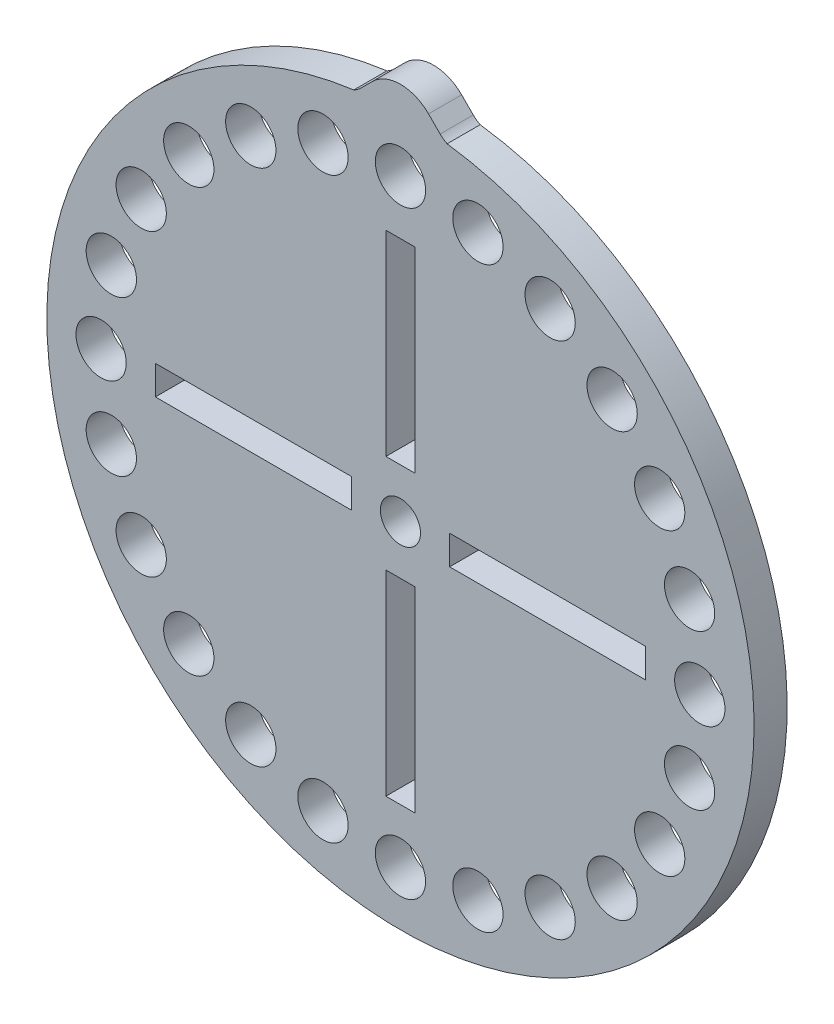
SolidWorks part; units mm, degrees
ref_plane "Front Plane" through (0, 0, 0) normal (0, 0, 1) x (1, 0, 0)
ref_plane "Top Plane" through (0, 0, 0) normal (0, 1, 0) x (1, 0, 0)
ref_plane "Right Plane" through (0, 0, 0) normal (1, 0, 0) x (0, 0, -1)
sketch "Sketch1" plane through (0, 0, 0) normal (0, 0, 1) x (1, 0, 0)
  line L0 (0, 31.26) -> (0, 33.8) construction
  line L1 (0, 28.72) -> (2.5183, 28.3885) construction
  line L2 (2.5183, 28.3885) -> (4.915, 28.0729) construction
  line L3 (4.915, 28.0729) -> (7.4333, 27.7414) construction
  line L4 (0, 2.05) -> (0, 4.59) construction
  line L5 (-0.1778, 26.1862) -> (0.1778, 26.1862) construction
  line L6 (-0.1778, 26.1862) -> (-0.1778, 30.9862) construction
  line L7 (-0.1778, 30.9862) -> (0.1778, 30.9862) construction
  line L8 (0.1778, 26.1862) -> (0.1778, 30.9862) construction
  line L9 (-1.524, 23.64) -> (1.524, 23.64)
  line L10 (-1.524, 23.64) -> (-1.524, 4.59)
  line L11 (-1.524, 4.59) -> (1.524, 4.59)
  line L12 (1.524, 23.64) -> (1.524, 4.59)
  line L13 (0, 26.18) -> (0, 23.64) construction
  line L14 (23.64, 1.524) -> (23.64, -1.524)
  line L15 (23.64, 1.524) -> (4.59, 1.524)
  line L16 (23.64, -1.524) -> (4.59, -1.524)
  line L17 (4.59, 1.524) -> (4.59, -1.524)
  line L18 (1.524, -23.64) -> (-1.524, -23.64)
  line L19 (1.524, -23.64) -> (1.524, -4.59)
  line L20 (-1.524, -23.64) -> (-1.524, -4.59)
  line L21 (1.524, -4.59) -> (-1.524, -4.59)
  line L22 (-23.64, -1.524) -> (-23.64, 1.524)
  line L23 (-23.64, -1.524) -> (-4.59, -1.524)
  line L24 (-23.64, 1.524) -> (-4.59, 1.524)
  line L25 (-4.59, -1.524) -> (-4.59, 1.524)
  circle A0 centre (0, 0) radius 33.8
  circle A1 centre (14.36, 24.8722) radius 2.54
  circle A2 centre (20.3081, 20.3081) radius 2.54
  circle A3 centre (24.8722, 14.36) radius 2.54
  circle A4 centre (27.7414, 7.4333) radius 2.54
  circle A5 centre (28.72, 0) radius 2.54
  circle A6 centre (27.7414, -7.4333) radius 2.54
  circle A7 centre (24.8722, -14.36) radius 2.54
  circle A8 centre (20.3081, -20.3081) radius 2.54
  circle A9 centre (14.36, -24.8722) radius 2.54
  circle A10 centre (7.4333, -27.7414) radius 2.54
  circle A11 centre (0, -28.72) radius 2.54
  circle A12 centre (-7.4333, -27.7414) radius 2.54
  circle A13 centre (-14.36, -24.8722) radius 2.54
  circle A14 centre (-20.3081, -20.3081) radius 2.54
  circle A15 centre (-24.8722, -14.36) radius 2.54
  circle A16 centre (-27.7414, -7.4333) radius 2.54
  circle A17 centre (-28.72, 0) radius 2.54
  circle A18 centre (-27.7414, 7.4333) radius 2.54
  circle A19 centre (-24.8722, 14.36) radius 2.54
  circle A20 centre (-20.3081, 20.3081) radius 2.54
  circle A21 centre (-14.36, 24.8722) radius 2.54
  circle A22 centre (-7.4333, 27.7414) radius 2.54
  circle A23 centre (0, 28.72) radius 2.54
  circle A24 centre (7.4333, 27.7414) radius 2.54
  circle A25 centre (0, 0) radius 2.05
  point P54 (0, 0)
  point P84 (0, 0)
  dimension "D1" = 5.08
  dimension "D3" = 2.54
  dimension "D5" = 4.1
  dimension "D6" = 67.6
  dimension "D4" = 3.048
  dimension "D8" = 4.8
  dimension "D9" = 0.3556
  dimension "D10" = 2.54
  dimension "D11" = 19.05
  dimension "D7" = 4
  dimension "D2" = 24
extrude "Boss-Extrude1" add sketch "Sketch1" along normal blind 3.175
sketch "Sketch3" plane through (0, 0, 0) normal (0, 0, 1) x (1, 0, 0)
  line L0 (0, 33.8) -> (0, 35.2241) construction
  line L1 (2.6941, 35.2241) -> (-2.6941, 35.2241) construction
  line L2 (-2.6941, 35.2241) -> (-4.4066, 33.5115)
  line L3 (2.6941, 35.2241) -> (4.4066, 33.5115)
  line L4 (4.4066, 33.5115) -> (-4.4066, 33.5115) construction
  arc A0 (2.6941, 35.2241) -> (-2.6941, 35.2241) centre (0, 32.53) ccw
  circle A1 centre (0, 0) radius 33.8
  arc A2 (4.4066, 33.5115) -> (-4.4066, 33.5115) centre (0, 0) ccw
  circle A3 centre (0, 0) radius 33.8 construction
  point P9 (0, 35.2241)
  dimension "D2" = 3.81
  dimension "D3" = 2.54
  dimension "D4" = 90
  dimension "D1" = 0
extrude "Boss-Extrude2" add sketch "Sketch3" along normal up to surface (3.175 mm away) up to face at (9.9733, 27.7414, 3.175)
fillet "Fillet1" radius 2.54 2 edges at (-4.4066, 33.5115, 1.5875) (4.4066, 33.5115, 1.5875)
sketch "Sketch4" plane through (0, 0, 0) normal (0, 0, 1) x (1, 0, 0)
  line L0 (-1.397, -23.513) -> (1.397, -23.513)
  line L1 (1.397, -23.513) -> (1.397, -4.717)
  line L2 (1.397, -4.717) -> (-1.397, -4.717)
  line L3 (-1.397, -4.717) -> (-1.397, -23.513)
  line L4 (-1.524, -23.64) -> (1.524, -23.64)
  line L5 (-1.524, -4.59) -> (-1.524, -23.64)
  line L6 (1.524, -4.59) -> (-1.524, -4.59)
  line L7 (1.524, -23.64) -> (1.524, -4.59)
  line L8 (-1.524, -23.64) -> (1.524, -23.64) construction
  line L9 (-1.524, -4.59) -> (-1.524, -23.64) construction
  line L10 (1.524, -4.59) -> (-1.524, -4.59) construction
  line L11 (1.524, -23.64) -> (1.524, -4.59) construction
  line L12 (23.64, -1.524) -> (23.64, 1.524)
  line L13 (4.59, -1.524) -> (23.64, -1.524)
  line L14 (4.59, 1.524) -> (4.59, -1.524)
  line L15 (23.64, 1.524) -> (4.59, 1.524)
  line L16 (23.64, -1.524) -> (23.64, 1.524) construction
  line L17 (4.59, -1.524) -> (23.64, -1.524) construction
  line L18 (4.59, 1.524) -> (4.59, -1.524) construction
  line L19 (23.64, 1.524) -> (4.59, 1.524) construction
  line L20 (1.524, 23.64) -> (-1.524, 23.64)
  line L21 (-1.524, 23.64) -> (-1.524, 4.59)
  line L22 (-1.524, 4.59) -> (1.524, 4.59)
  line L23 (1.524, 4.59) -> (1.524, 23.64)
  line L24 (1.524, 23.64) -> (-1.524, 23.64) construction
  line L25 (-1.524, 23.64) -> (-1.524, 4.59) construction
  line L26 (-1.524, 4.59) -> (1.524, 4.59) construction
  line L27 (1.524, 4.59) -> (1.524, 23.64) construction
  line L28 (-23.64, 1.524) -> (-23.64, -1.524)
  line L29 (-4.59, 1.524) -> (-23.64, 1.524)
  line L30 (-4.59, -1.524) -> (-4.59, 1.524)
  line L31 (-23.64, -1.524) -> (-4.59, -1.524)
  line L32 (-23.64, 1.524) -> (-23.64, -1.524) construction
  line L33 (-4.59, 1.524) -> (-23.64, 1.524) construction
  line L34 (-4.59, -1.524) -> (-4.59, 1.524) construction
  line L35 (-23.64, -1.524) -> (-4.59, -1.524) construction
  line L36 (23.513, -1.397) -> (23.513, 1.397)
  line L37 (23.513, 1.397) -> (4.717, 1.397)
  line L38 (4.717, 1.397) -> (4.717, -1.397)
  line L39 (4.717, -1.397) -> (23.513, -1.397)
  line L40 (1.397, 23.513) -> (-1.397, 23.513)
  line L41 (-1.397, 23.513) -> (-1.397, 4.717)
  line L42 (-1.397, 4.717) -> (1.397, 4.717)
  line L43 (1.397, 4.717) -> (1.397, 23.513)
  line L44 (-23.513, 1.397) -> (-23.513, -1.397)
  line L45 (-23.513, -1.397) -> (-4.717, -1.397)
  line L46 (-4.717, -1.397) -> (-4.717, 1.397)
  line L47 (-4.717, 1.397) -> (-23.513, 1.397)
  circle A0 centre (0, 0) radius 33.927
  circle A1 centre (28.72, 0) radius 2.54
  circle A2 centre (28.72, 0) radius 2.54 construction
  circle A3 centre (27.7414, 7.4333) radius 2.54
  circle A4 centre (27.7414, 7.4333) radius 2.54 construction
  circle A5 centre (24.8722, 14.36) radius 2.54
  circle A6 centre (24.8722, 14.36) radius 2.54 construction
  circle A7 centre (20.3081, 20.3081) radius 2.54
  circle A8 centre (20.3081, 20.3081) radius 2.54 construction
  circle A9 centre (14.36, 24.8722) radius 2.667
  circle A10 centre (14.36, 24.8722) radius 2.667 construction
  circle A11 centre (0, 0) radius 33.8
  circle A12 centre (0, 0) radius 33.8 construction
  circle A13 centre (-14.36, -24.8722) radius 2.54
  circle A14 centre (-14.36, -24.8722) radius 2.54 construction
  circle A15 centre (-7.4333, -27.7414) radius 2.54
  circle A16 centre (-7.4333, -27.7414) radius 2.54 construction
  circle A17 centre (0, -28.72) radius 2.54
  circle A18 centre (0, -28.72) radius 2.54 construction
  circle A19 centre (7.4333, -27.7414) radius 2.54
  circle A20 centre (7.4333, -27.7414) radius 2.54 construction
  circle A21 centre (14.36, -24.8722) radius 2.54
  circle A22 centre (14.36, -24.8722) radius 2.54 construction
  circle A23 centre (20.3081, -20.3081) radius 2.54
  circle A24 centre (20.3081, -20.3081) radius 2.54 construction
  circle A25 centre (24.8722, -14.36) radius 2.54
  circle A26 centre (24.8722, -14.36) radius 2.54 construction
  circle A27 centre (27.7414, -7.4333) radius 2.54
  circle A28 centre (27.7414, -7.4333) radius 2.54 construction
  circle A29 centre (-14.36, 24.8722) radius 2.54
  circle A30 centre (-14.36, 24.8722) radius 2.54 construction
  circle A31 centre (-20.3081, 20.3081) radius 2.54
  circle A32 centre (-20.3081, 20.3081) radius 2.54 construction
  circle A33 centre (-24.8722, 14.36) radius 2.54
  circle A34 centre (-24.8722, 14.36) radius 2.54 construction
  circle A35 centre (-27.7414, 7.4333) radius 2.54
  circle A36 centre (-27.7414, 7.4333) radius 2.54 construction
  circle A37 centre (-28.72, 0) radius 2.54
  circle A38 centre (-28.72, 0) radius 2.54 construction
  circle A39 centre (-27.7414, -7.4333) radius 2.54
  circle A40 centre (-27.7414, -7.4333) radius 2.54 construction
  circle A41 centre (-24.8722, -14.36) radius 2.54
  circle A42 centre (-24.8722, -14.36) radius 2.54 construction
  circle A43 centre (-20.3081, -20.3081) radius 2.54
  circle A44 centre (-20.3081, -20.3081) radius 2.54 construction
  circle A45 centre (0, 0) radius 2.05
  circle A46 centre (0, 0) radius 2.05 construction
  circle A47 centre (7.4333, 27.7414) radius 2.54
  circle A48 centre (7.4333, 27.7414) radius 2.54 construction
  circle A49 centre (0, 28.72) radius 2.54
  circle A50 centre (0, 28.72) radius 2.54 construction
  circle A51 centre (-7.4333, 27.7414) radius 2.54
  circle A52 centre (-7.4333, 27.7414) radius 2.54 construction
  circle A53 centre (28.72, 0) radius 2.413
  circle A54 centre (27.7414, 7.4333) radius 2.413
  circle A55 centre (24.8722, 14.36) radius 2.413
  circle A56 centre (20.3081, 20.3081) radius 2.413
  circle A57 centre (14.36, 24.8722) radius 2.54 construction
  circle A58 centre (-14.36, -24.8722) radius 2.413
  circle A59 centre (-7.4333, -27.7414) radius 2.413
  circle A60 centre (0, -28.72) radius 2.413
  circle A61 centre (7.4333, -27.7414) radius 2.413
  circle A62 centre (14.36, -24.8722) radius 2.413
  circle A63 centre (20.3081, -20.3081) radius 2.413
  circle A64 centre (24.8722, -14.36) radius 2.413
  circle A65 centre (27.7414, -7.4333) radius 2.413
  circle A66 centre (-14.36, 24.8722) radius 2.413
  circle A67 centre (-20.3081, 20.3081) radius 2.413
  circle A68 centre (-24.8722, 14.36) radius 2.413
  circle A69 centre (-27.7414, 7.4333) radius 2.413
  circle A70 centre (-28.72, 0) radius 2.413
  circle A71 centre (-27.7414, -7.4333) radius 2.413
  circle A72 centre (-24.8722, -14.36) radius 2.413
  circle A73 centre (-20.3081, -20.3081) radius 2.413
  circle A74 centre (0, 0) radius 1.923
  circle A75 centre (7.4333, 27.7414) radius 2.413
  circle A76 centre (0, 28.72) radius 2.413
  circle A77 centre (-7.4333, 27.7414) radius 2.413
  circle A78 centre (14.36, 24.8722) radius 2.413
  dimension "D1" = 0
  dimension "D2" = 0
  dimension "D3" = 0
  dimension "D4" = 0
  dimension "D5" = 0.127
  dimension "D6" = 0
  dimension "D7" = 0
  dimension "D8" = 0
  dimension "D9" = 0
  dimension "D10" = 0
  dimension "D11" = 0
  dimension "D12" = 0
  dimension "D13" = 0
  dimension "D14" = 0
  dimension "D15" = 0
  dimension "D16" = 0
  dimension "D17" = 0
  dimension "D18" = 0
  dimension "D19" = 0
  dimension "D20" = 0
  dimension "D21" = 0
  dimension "D22" = 0
  dimension "D23" = 0
  dimension "D24" = 0
  dimension "D25" = 0
  dimension "D26" = 0
  dimension "D27" = 0
  dimension "D28" = 0
  dimension "D29" = 0
  dimension "D30" = 0
  dimension "D31" = 0.127
  dimension "D32" = 0.127
  dimension "D33" = 0.127
extrude "Kerf Adjustment" add sketch "Sketch4" along normal blind 3.175
equation "\"kerf_adjustment\"= .005"
equation "\"D32@Sketch4\"= \"kerf_adjustment\""
equation "\"D31@Sketch4\" = \"kerf_adjustment\""
equation "\"D33@Sketch4\"= \"kerf_adjustment\""
